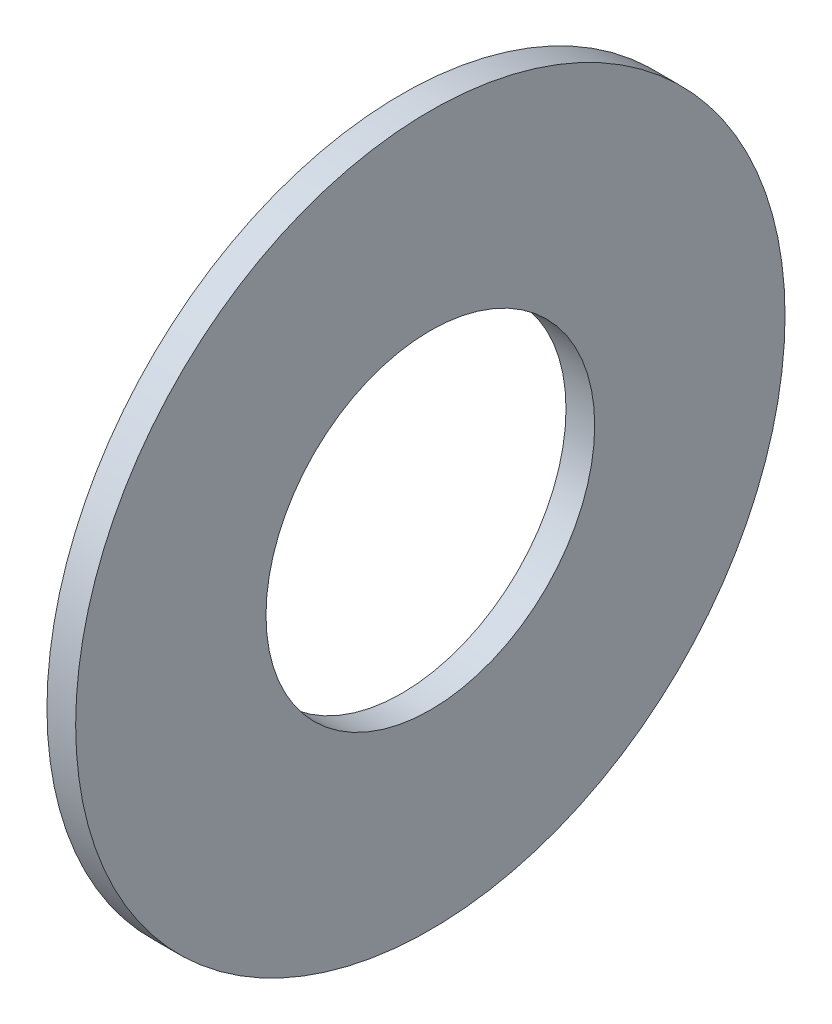
SolidWorks part; units mm, degrees
ref_plane "Plane1" through (0, 0, 0) normal (0, 0, 1) x (1, 0, 0)
ref_plane "Plane2" through (0, 0, 0) normal (0, 1, 0) x (1, 0, 0)
ref_plane "Plane3" through (0, 0, 0) normal (1, 0, 0) x (0, 0, -1)
sketch "Sketch1" plane through (0, 0, 0) normal (0, 0, 1) x (1, 0, 0)
  line L0 (-34.925, 0) -> (9.525, 0) construction
  line L1 (0, 26.1874) -> (0, 56.515)
  line L2 (0, 56.515) -> (-4.572, 56.515)
  line L3 (-4.572, 56.515) -> (-4.572, 26.1874)
  line L4 (-4.572, 26.1874) -> (0, 26.1874)
  dimension "Thickness" = 4.572
  dimension "Inside_dia" = 52.3748
  dimension "Outside_dia" = 113.03
revolve "Base-Revolve" add sketch "Sketch1" angle 360 about L0
